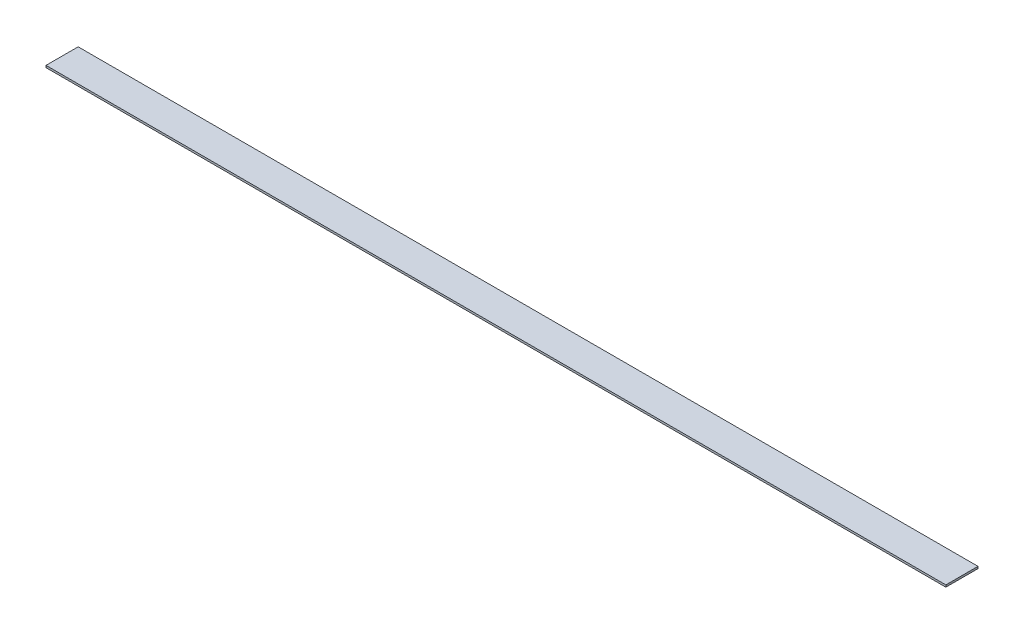
SolidWorks part; units mm, degrees
ref_plane "Front Plane" through (0, 0, 0) normal (0, 0, 1) x (1, 0, 0)
ref_plane "Top Plane" through (0, 0, 0) normal (0, 1, 0) x (1, 0, 0)
ref_plane "Right Plane" through (0, 0, 0) normal (1, 0, 0) x (0, 0, -1)
sketch "Sketch1" plane through (0, 0, 0) normal (0, 1, 0) x (1, 0, 0)
  line L1 (0, 0) -> (711.2, 0)
  line L2 (0, 0) -> (0, 25.4)
  line L3 (0, 25.4) -> (711.2, 25.4)
  line L4 (711.2, 0) -> (711.2, 25.4)
  dimension "D1" = 25.4
  dimension "D2" = 711.2
extrude "Boss-Extrude1" add sketch "Sketch1" along normal blind 1.5875
